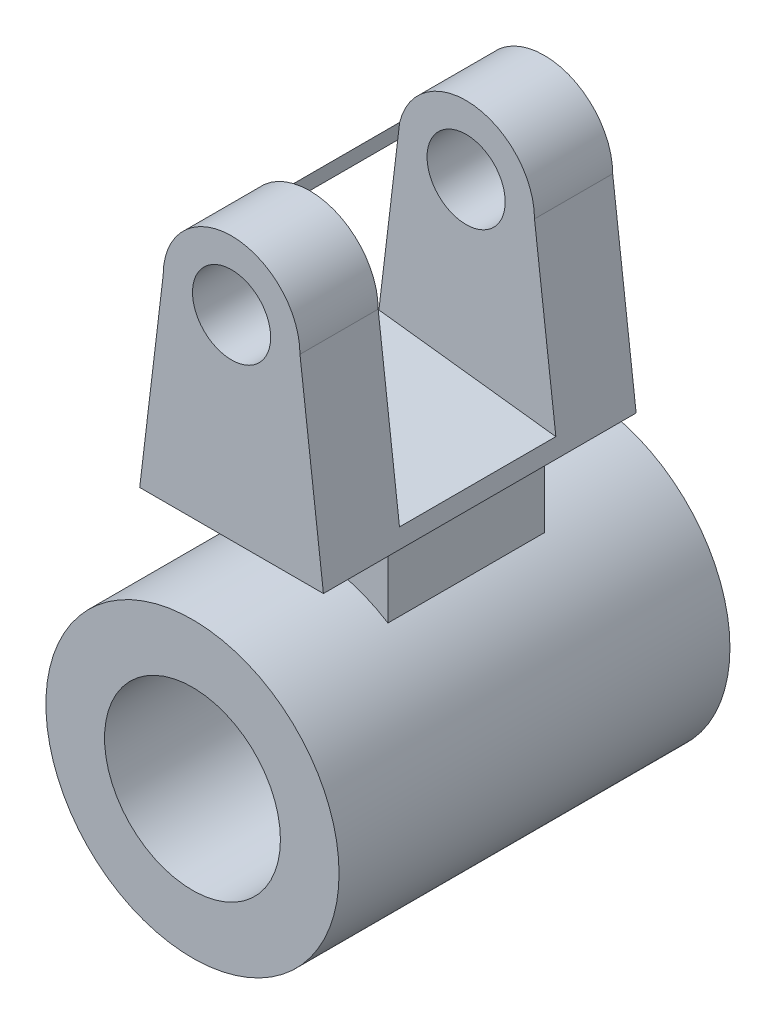
SolidWorks part; units mm, degrees
ref_plane "Front Plane" through (0, 0, 0) normal (0, 0, 1) x (1, 0, 0)
ref_plane "Top Plane" through (0, 0, 0) normal (0, 1, 0) x (1, 0, 0)
ref_plane "Right Plane" through (0, 0, 0) normal (1, 0, 0) x (0, 0, -1)
sketch "Sketch1" plane through (0, 0, 0) normal (0, 0, 1) x (1, 0, 0)
  circle A0 centre (0, 0) radius 22.5
  circle A1 centre (0, 0) radius 37.5
  dimension "D1" = 75
  dimension "D2" = 45
extrude "Boss-Extrude1" add sketch "Sketch1" along normal mid plane 100
sketch "Sketch3" plane through (0, 0, 0) normal (0, 0, 1) x (1, 0, 0)
  line L0 (0, 168.9665) -> (0, -141.845) construction
  line L1 (-289.1144, 0) -> (263.0778, 0) construction
  line L2 (-23.5, 50) -> (23.5, 50)
  line L3 (-17.5, 100) -> (-23.5, 50)
  line L4 (17.5, 100) -> (23.5, 50)
  circle A0 centre (0, 100) radius 10
  arc A1 (17.5, 100) -> (-17.5, 100) centre (0, 100) ccw
  point P2 (0, 117.5)
  dimension "D1" = 35
  dimension "D2" = 20
  dimension "D3" = 47
  dimension "D4" = 100
  dimension "D5" = 67.5
extrude "Boss-Extrude3" add sketch "Sketch3" along normal mid plane 80 separate body contours L4 L2 L3 A1
sketch "Sketch10" plane through (0, 0, 40) normal (0, 0, 1) x (1, 0, 0)
  circle A0 centre (0, 100) radius 10
  dimension "D1" = 20
extrude "Cut-Extrude5" cut sketch "Sketch10" against normal through all
sketch "Sketch11" plane through (-29.0812, 3.4897, 0) normal (-0.9929, 0.1191, 0) x (0, 0, 1)
  line L0 (40, 116.7877) -> (-40, 116.7877) construction
  line L1 (-20, 116.7877) -> (20, 116.7877)
  line L2 (-20, 116.7877) -> (-20, 56.8439)
  line L3 (-20, 56.8439) -> (20, 56.8439)
  line L4 (20, 116.7877) -> (20, 56.8439)
  line L5 (40, 46.8439) -> (-40, 46.8439) construction
  line L6 (40, 97.2026) -> (40, 46.8439) construction
  line L7 (-40, 97.2026) -> (-40, 46.8439) construction
  dimension "D1" = 10
  dimension "D2" = 20
  dimension "D3" = 20
  dimension "D4" = 59.9438
extrude "Cut-Extrude6" cut sketch "Sketch11" against normal through all
sketch "Sketch12" plane through (0, 0, 0) normal (0, 0, 1) x (1, 0, 0)
  line L0 (0, 124.08) -> (0, -47.4693) construction
  line L1 (-20, 50) -> (20, 50)
  line L2 (-20, 50) -> (-20, 30)
  line L3 (-20, 30) -> (20, 30)
  line L4 (20, 50) -> (20, 30)
  dimension "D1" = 20
  dimension "D2" = 20
  dimension "D3" = 50
  dimension "D4" = 20
extrude "Boss-Extrude8" add sketch "Sketch12" along normal mid plane 40
